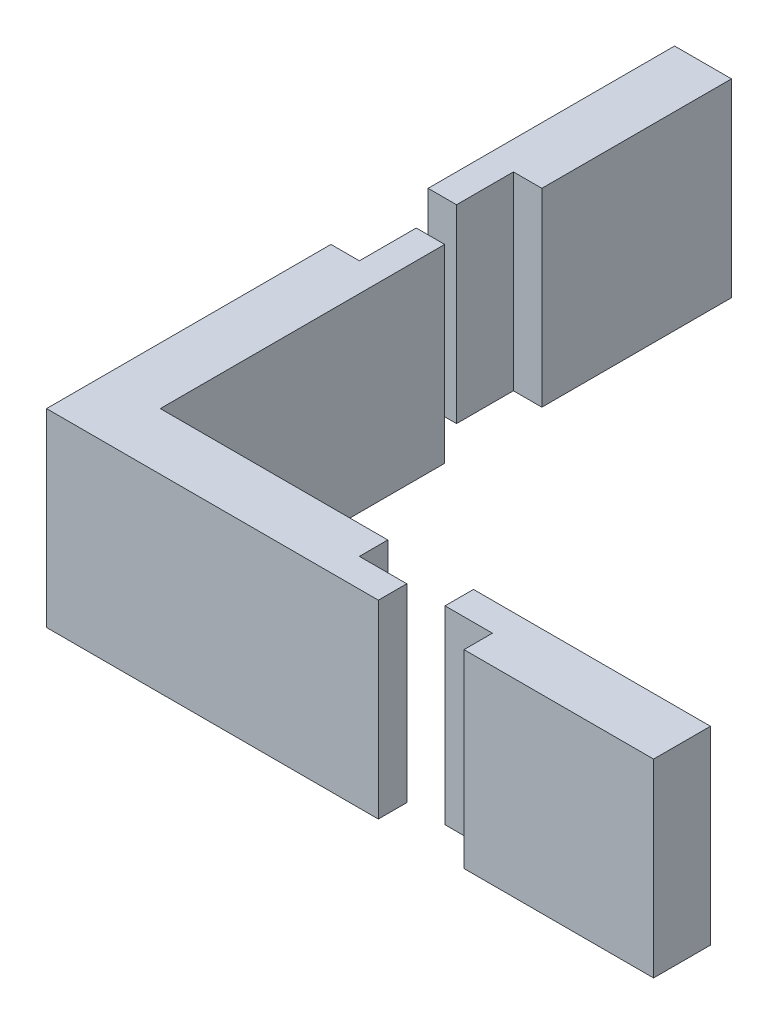
SolidWorks part; units mm, degrees
ref_plane "Front Plane" through (0, 0, 0) normal (0, 0, 1) x (1, 0, 0)
ref_plane "Top Plane" through (0, 0, 0) normal (0, 1, 0) x (1, 0, 0)
ref_plane "Right Plane" through (0, 0, 0) normal (1, 0, 0) x (0, 0, -1)
sketch "Sketch1" plane through (0, 0, 0) normal (0, 1, 0) x (1, 0, 0)
  line L1 (-1.5, 7.5) -> (1.5, 7.5)
  line L2 (-1.5, 7.5) -> (-1.5, -7.5)
  line L3 (-1.5, -7.5) -> (1.5, -7.5)
  line L4 (1.5, 7.5) -> (1.5, -7.5)
  line L5 (-1.5, 7.5) -> (1.5, -7.5) construction
  line L6 (-1.5, -7.5) -> (1.5, 7.5) construction
  line L7 (1.5, 7.5) -> (0, 7.5)
  line L8 (1.5, 7.5) -> (1.5, 10.5)
  line L9 (1.5, 10.5) -> (0, 10.5)
  line L10 (0, 7.5) -> (0, 10.5)
  line L11 (1.5, -7.5) -> (13.5, -7.5)
  line L12 (1.5, -7.5) -> (1.5, -4.5)
  line L13 (1.5, -4.5) -> (13.5, -4.5)
  line L14 (13.5, -7.5) -> (13.5, -4.5)
  line L15 (13.5, -7.5) -> (16, -7.5)
  line L16 (13.5, -7.5) -> (13.5, -6)
  line L17 (13.5, -6) -> (16, -6)
  line L18 (16, -7.5) -> (16, -6)
  line L19 (20.5178, -6) -> (18.0178, -6)
  line L20 (20.5178, -6) -> (20.5178, -4.5)
  line L21 (20.5178, -4.5) -> (18.0178, -4.5)
  line L22 (18.0178, -6) -> (18.0178, -4.5)
  line L23 (20.5178, -4.5) -> (30.5178, -4.5)
  line L24 (20.5178, -4.5) -> (20.5178, -7.5)
  line L25 (20.5178, -7.5) -> (30.5178, -7.5)
  line L26 (30.5178, -4.5) -> (30.5178, -7.5)
  line L27 (0, 12.6251) -> (-1.5, 12.6251)
  line L28 (0, 12.6251) -> (0, 15.6251)
  line L29 (0, 15.6251) -> (-1.5, 15.6251)
  line L30 (-1.5, 12.6251) -> (-1.5, 15.6251)
  line L31 (-1.5, 15.6251) -> (1.5, 15.6251)
  line L32 (-1.5, 15.6251) -> (-1.5, 25.6251)
  line L33 (-1.5, 25.6251) -> (1.5, 25.6251)
  line L34 (1.5, 15.6251) -> (1.5, 25.6251)
  point P0 (0, 0)
  dimension "D1" = 3
  dimension "D2" = 15
  dimension "D3" = 1.5
  dimension "D4" = 3
  dimension "D5" = 3
  dimension "D6" = 12
  dimension "D7" = 1.5
  dimension "D8" = 2.5
  dimension "D9" = 2.5
  dimension "D10" = 1.5
  dimension "D11" = 3
  dimension "D12" = 10
  dimension "D13" = 3
  dimension "D14" = 1.5
  dimension "D15" = 10
  dimension "D16" = 3
extrude "Boss-Extrude2" add sketch "Sketch1" along normal blind 10 contours L31 L34 L33 L32 L29 | L30 L27 L28 L29 | L10 L1 L8 L9 | L4 L1 L2 L3 | L11 L14 L13 L4 | L22 L19 L20 L21 | L26 L23 L20 L24 L25 | L16 L17 L18 L15
